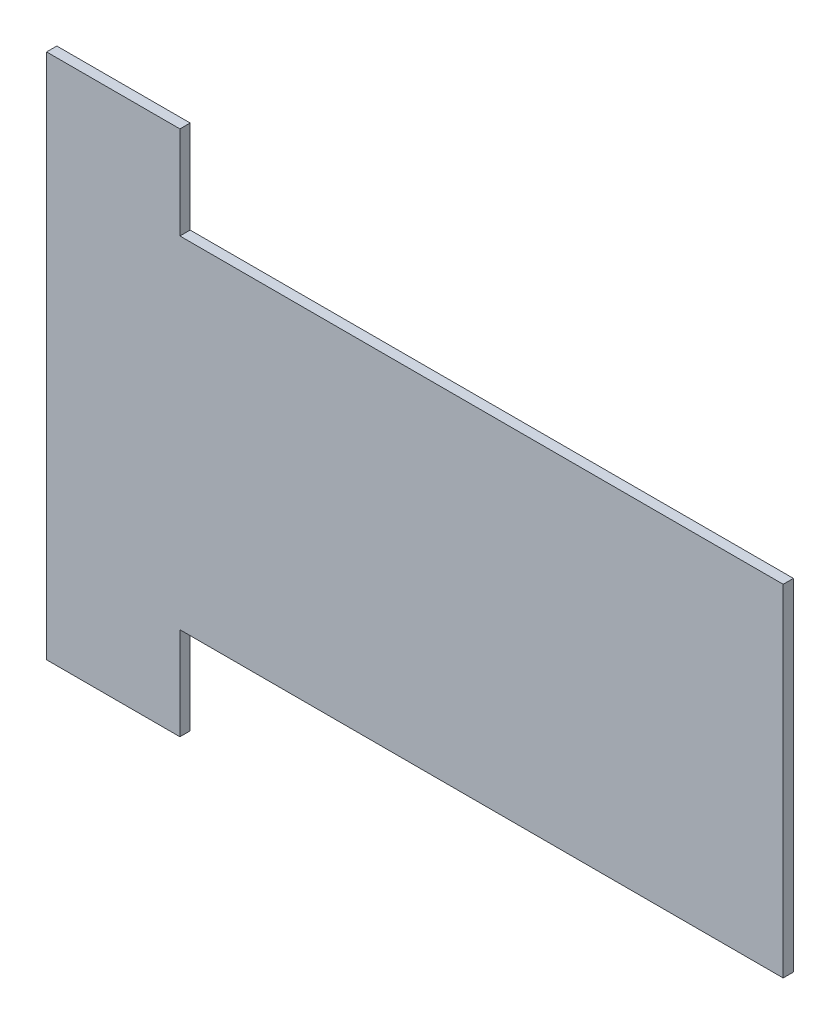
SolidWorks part; units mm, degrees
ref_plane "Front" through (0, 0, 0) normal (0, 0, 1) x (1, 0, 0)
ref_plane "Top" through (0, 0, 0) normal (0, 1, 0) x (1, 0, 0)
ref_plane "Right" through (0, 0, 0) normal (1, 0, 0) x (0, 0, -1)
sketch "Sketch1" plane through (0, 0, 0) normal (0, 0, 1) x (1, 0, 0)
  line L0 (218, -557.5) -> (218, -860.775)
  line L1 (218, 860.775) -> (-218, 860.775)
  line L2 (218, 860.775) -> (218, 557.5)
  line L3 (218, -860.775) -> (-218, -860.775)
  line L4 (-218, 860.775) -> (-218, -860.775)
  line L5 (218, 860.775) -> (-218, -860.775) construction
  line L6 (218, -860.775) -> (-218, 860.775) construction
  line L7 (218, -557.5) -> (2190.65, -557.5)
  line L9 (218, 557.5) -> (2190.65, 557.5)
  line L10 (2190.65, -557.5) -> (2190.65, 557.5)
  point P0 (0, 0)
  point P10 (2190.65, 0)
  point P11 (0, 0)
  dimension "D1" = 1721.55
  dimension "D2" = 436
  dimension "D3" = 1972.65
  dimension "D4" = 1115
extrude "Boss-Extrude1" add sketch "Sketch1" along normal blind 33.45
